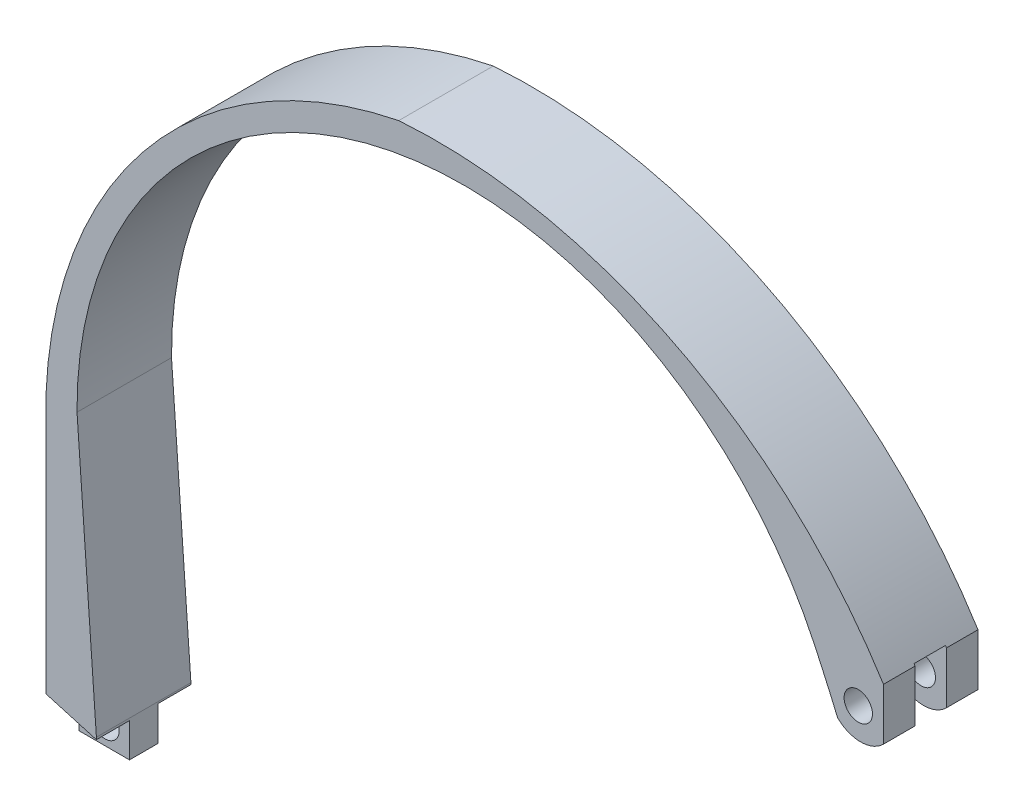
SolidWorks part; units mm, degrees
ref_plane "Front Plane" through (0, 0, 0) normal (0, 0, 1) x (1, 0, 0)
ref_plane "Top Plane" through (0, 0, 0) normal (0, 1, 0) x (1, 0, 0)
ref_plane "Right Plane" through (0, 0, 0) normal (1, 0, 0) x (0, 0, -1)
sketch "Sketch3" plane through (0, 0, 0) normal (0, 0, 1) x (1, 0, 0)
  line L0 (-83.2408, 45.6801) -> (-86.3182, 88.8069)
  line L1 (-91.2408, 47.6545) -> (-91.2408, 88.8069)
  line L2 (-91.2408, 47.6545) -> (-91.2408, 39.9314)
  line L4 (-83.2408, 39.9314) -> (-83.2408, 45.6801)
  line L5 (41.6818, 115.4125) -> (41.6818, 107.1807)
  line L6 (-91.2408, 39.9314) -> (-83.2408, 39.9314)
  arc A0 (-86.3182, 88.8069) -> (30.7176, 115.4125) centre (-24.8872, 89.2951) cw
  arc A1 (-91.2408, 88.8069) -> (-35.2516, 154.4289) centre (-21.5663, 86.0562) cw
  arc A2 (-35.2516, 154.4289) -> (41.6818, 115.4125) centre (-29.2118, 70.9806) cw
  arc A3 (30.7176, 115.4125) -> (34.3921, 107.1807) centre (-180.9922, 15.973) cw
  arc A6 (34.3921, 107.1807) -> (41.6818, 107.1807) centre (38.0369, 110.8256) ccw
  circle A7 centre (-87.1256, 43.1305) radius 2.25
  circle A8 centre (37.6818, 110.447) radius 2.25
extrude "Boss-Extrude1" add sketch "Sketch3" against normal blind 15
sketch "Sketch5" plane through (0, 0, 0) normal (0, 0, 1) x (1, 0, 0)
  line L9 (-91.2408, 47.6347) -> (-83.2408, 45.336)
  line L10 (-91.2408, 88.8069) -> (-91.2408, 39.9314) construction
  line L11 (-83.2408, 39.9314) -> (-83.2408, 45.6801) construction
  line L12 (-83.2408, 45.336) -> (-83.2408, 39.9314)
  line L13 (-83.2408, 39.9314) -> (-91.2408, 39.9314)
  line L14 (-91.2408, 39.9314) -> (-91.2408, 47.6347)
extrude "Cut-Extrude2" cut sketch "Sketch5" against normal blind 5.25
sketch "Sketch7" plane through (0, 0, -15) normal (0, 0, -1) x (-1, 0, 0)
  line L0 (91.2408, 47.6545) -> (88.2799, 46.8401)
  line L6 (83.2408, 45.6801) -> (83.2408, 39.9314)
  line L7 (83.2408, 45.6801) -> (83.2408, 39.9314)
  line L8 (83.2408, 39.9314) -> (91.2408, 39.9314)
  line L10 (91.2408, 39.9314) -> (91.2408, 88.8069)
  line L11 (91.2408, 39.9314) -> (91.2408, 88.8069)
  line L12 (-41.6818, 115.4125) -> (-41.6818, 107.1807)
  line L13 (86.3182, 88.8069) -> (83.2408, 45.6801)
  line L20 (86.3182, 88.8069) -> (83.2408, 45.6801)
  line L21 (-41.6818, 115.4125) -> (-41.6818, 107.1807)
  line L22 (83.2408, 39.9314) -> (91.2408, 39.9314)
  arc A2 (91.2408, 88.8069) -> (35.2516, 154.4289) centre (21.5663, 86.0562) ccw
  arc A3 (91.2408, 88.8069) -> (35.2516, 154.4289) centre (21.5663, 86.0562) ccw
  arc A10 (35.2516, 154.4289) -> (-41.6818, 115.4125) centre (29.2118, 70.9806) ccw
  arc A14 (35.2516, 154.4289) -> (-41.6818, 115.4125) centre (29.2118, 70.9806) ccw
  arc A15 (-41.6818, 107.1807) -> (-34.3921, 107.1807) centre (-38.0369, 110.8256) ccw
  arc A16 (-41.6818, 107.1807) -> (-34.3921, 107.1807) centre (-38.0369, 110.8256) ccw
  arc A17 (-30.7176, 115.4125) -> (-34.3921, 107.1807) centre (180.9922, 15.973) ccw
  arc A18 (-30.7176, 115.4125) -> (-34.3921, 107.1807) centre (180.9922, 15.973) ccw
  arc A19 (86.3182, 88.8069) -> (-30.7176, 115.4125) centre (24.8872, 89.2951) ccw
  arc A20 (86.3182, 88.8069) -> (-30.7176, 115.4125) centre (24.8872, 89.2951) ccw
  dimension "D1" = 0
sketch "Sketch8" plane through (0, 0, -15) normal (0, 0, -1) x (-1, 0, 0)
  line L9 (91.2408, 47.7189) -> (83.2408, 45.4105)
  line L10 (91.2408, 88.8069) -> (91.2408, 39.9314) construction
  line L11 (83.2408, 39.9314) -> (83.2408, 45.6801) construction
  line L12 (83.2408, 45.4105) -> (83.2408, 39.9314)
  line L13 (83.2408, 39.9314) -> (91.2408, 39.9314)
  line L14 (91.2408, 39.9314) -> (91.2408, 47.7189)
extrude "Cut-Extrude3" cut sketch "Sketch8" against normal blind 5.25
sketch "Sketch9" plane through (41.6818, 0, 0) normal (1, 0, 0) x (0, 0, -1)
  line L0 (0, 105.671) -> (15, 105.671) construction
  line L1 (5.0137, 115.671) -> (10, 115.671)
  line L2 (5.0137, 115.671) -> (5.0137, 105.671)
  line L3 (5.0137, 105.671) -> (10, 105.671)
  line L4 (10, 115.671) -> (10, 105.671)
  dimension "D1" = 10
extrude "Cut-Extrude4" cut sketch "Sketch9" against normal blind 20
